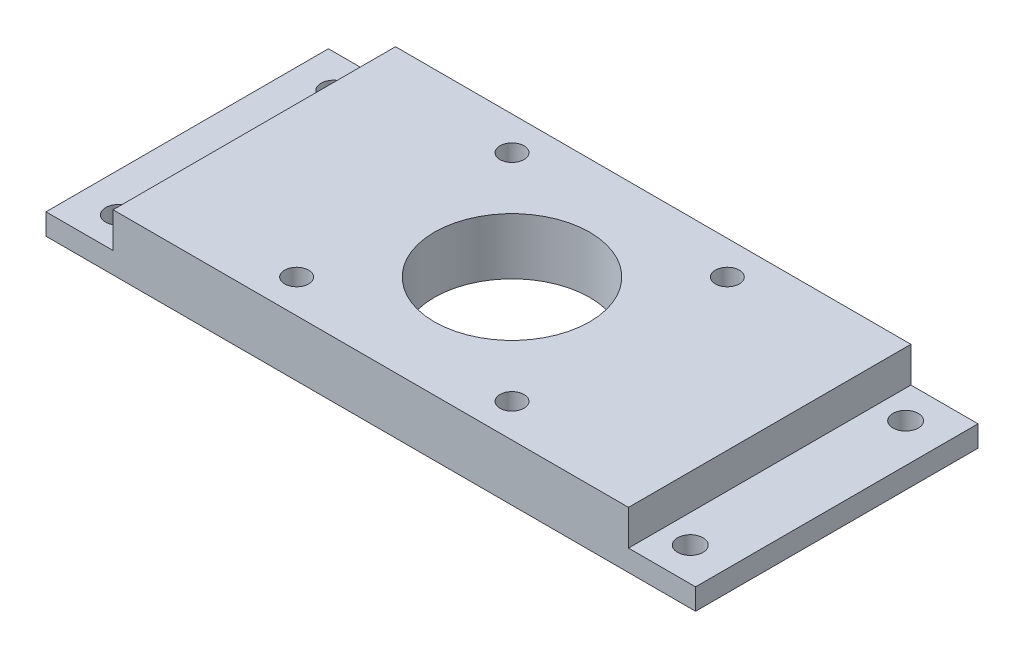
SolidWorks part; units mm, degrees
ref_plane "Front Plane" through (0, 0, 0) normal (0, 0, 1) x (1, 0, 0)
ref_plane "Top Plane" through (0, 0, 0) normal (0, 1, 0) x (1, 0, 0)
ref_plane "Right Plane" through (0, 0, 0) normal (1, 0, 0) x (0, 0, -1)
sketch "Sketch1" plane through (0, 0, 0) normal (0, 1, 0) x (1, 0, 0)
  line L1 (-36.5, -20) -> (36.5, -20)
  line L2 (-36.5, -20) -> (-36.5, 20)
  line L3 (-36.5, 20) -> (36.5, 20)
  line L4 (36.5, -20) -> (36.5, 20)
  line L5 (-36.5, -20) -> (36.5, 20) construction
  line L6 (-36.5, 20) -> (36.5, -20) construction
  point P0 (0, 0)
  dimension "D1" = 73
  dimension "D2" = 40
extrude "Boss-Extrude1" add sketch "Sketch1" along normal blind 5
sketch "Sketch2" plane through (0, 0, 0) normal (0, -1, 0) x (1, 0, 0)
  line L0 (-36.5, 20) -> (36.5, 20) construction
  line L1 (-46, -20) -> (46, -20)
  line L2 (-46, -20) -> (-46, 20)
  line L3 (-46, 20) -> (46, 20)
  line L4 (46, -20) -> (46, 20)
  line L5 (-46, -20) -> (46, 20) construction
  line L6 (-46, 20) -> (46, -20) construction
  point P0 (0, 0)
  dimension "D1" = 92
extrude "Boss-Extrude2" add sketch "Sketch2" along normal blind 3
sketch "Sketch3" plane through (0, 0, 0) normal (0, 1, 0) x (1, 0, 0)
  line L1 (-40.5, -15.25) -> (40.5, -15.25)
  line L2 (-40.5, -15.25) -> (-40.5, 15.25)
  line L3 (-40.5, 15.25) -> (40.5, 15.25)
  line L4 (40.5, -15.25) -> (40.5, 15.25)
  line L5 (-40.5, -15.25) -> (40.5, 15.25) construction
  line L6 (-40.5, 15.25) -> (40.5, -15.25) construction
  point P0 (0, 0)
  dimension "D1" = 30.5
  dimension "D2" = 81
hole_wizard "M3 Clearance Hole1" positions "Sketch4" profile "Sketch5" hole size "M3" standard "ANSI Metric" end condition through all
sketch "Sketch4" plane through (0, 0, 0) normal (0, 1, 0) x (1, 0, 0)
  point P0 (-40.5, 15.25)
  point P3 (-40.5, -15.25)
  point P6 (40.5, 15.25)
  point P9 (40.5, -15.25)
sketch "Sketch5" plane through (-40.5, 0, -15.25) normal (1, 0, 0) x (0, 0, 1)
  line L0 (0, 0) -> (0, 3)
  line L1 (0, 3) -> (1.8, 3)
  line L2 (1.8, 3) -> (1.8, 0)
  line L5 (1.8, 0) -> (0, 0)
  line L11 (0, -6.35) -> (0, 107.95) construction
  dimension "Thru Hole Dia." = 3.6
  dimension "Thru Hole Depth" = 3
hole_wizard "M3 Clearance Hole2" positions "Sketch6" profile "Sketch7" hole size "M3" standard "ANSI Metric" end condition through all
sketch "Sketch6" plane through (0, 5, 0) normal (0, 1, 0) x (1, 0, 0)
  line L1 (-15.25, -15.25) -> (15.25, -15.25)
  line L2 (-15.25, -15.25) -> (-15.25, 15.25)
  line L3 (-15.25, 15.25) -> (15.25, 15.25)
  line L4 (15.25, -15.25) -> (15.25, 15.25)
  line L5 (-15.25, -15.25) -> (15.25, 15.25) construction
  line L6 (-15.25, 15.25) -> (15.25, -15.25) construction
  point P1 (0, 0)
  point P2 (15.25, 15.25)
  point P61 (-15.25, -15.25)
  point P62 (-15.25, 15.25)
  point P63 (15.25, -15.25)
  dimension "D1" = 30.5
  dimension "D2" = 30.5
sketch "Sketch7" plane through (0, 5, 0) normal (1, 0, 0) x (0, 0, 1)
  line L0 (0, 0) -> (0, 8)
  line L1 (0, 8) -> (1.7, 8)
  line L2 (1.7, 8) -> (1.7, 0)
  line L5 (1.7, 0) -> (0, 0)
  line L11 (0, -6.35) -> (0, 107.95) construction
  dimension "Thru Hole Dia." = 3.4
  dimension "Thru Hole Depth" = 8
sketch "Sketch9" plane through (0, 5, 0) normal (0, 1, 0) x (1, 0, 0)
  circle A0 centre (0, 0) radius 11
  dimension "D1" = 22
extrude "Cut-Extrude1" cut sketch "Sketch9" against normal through all
equation "\"8`\"=84.8464"
